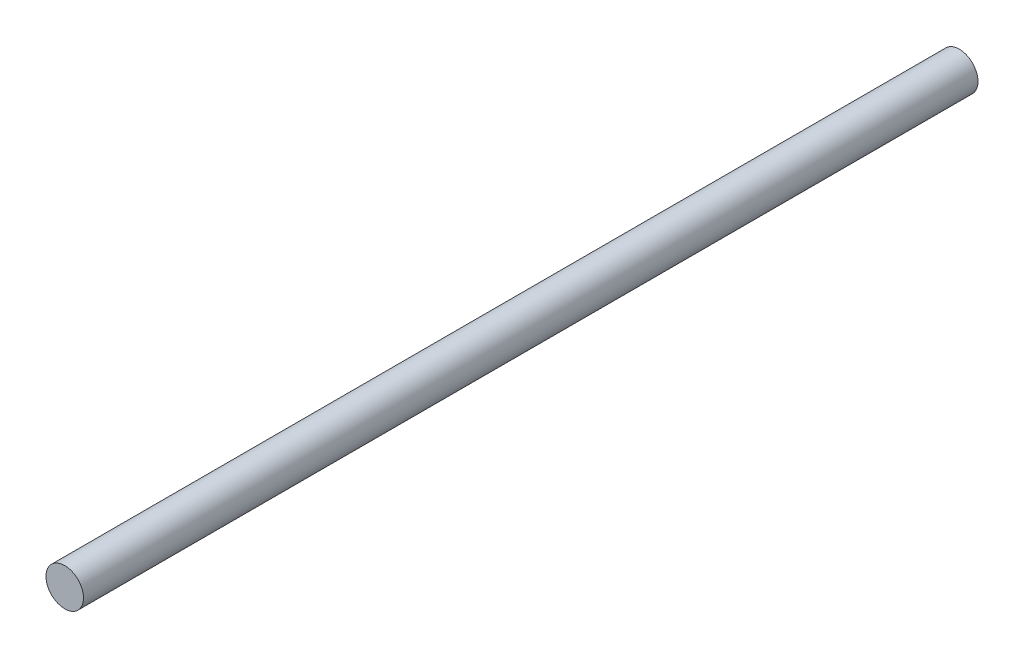
SolidWorks part; units mm, degrees
material "201 Annealed Stainless Steel (SS)"
ref_plane "Front Plane" through (0, 0, 0) normal (0, 0, 1) x (1, 0, 0)
ref_plane "Top Plane" through (0, 0, 0) normal (0, 1, 0) x (1, 0, 0)
ref_plane "Right Plane" through (0, 0, 0) normal (1, 0, 0) x (0, 0, -1)
sketch "Sketch1" plane through (0, 0, 0) normal (0, 0, 1) x (1, 0, 0)
  circle A0 centre (0, 0) radius 3.175
  dimension "D1" = 6.35
extrude "Boss-Extrude1" add sketch "Sketch1" along normal blind 151.384
